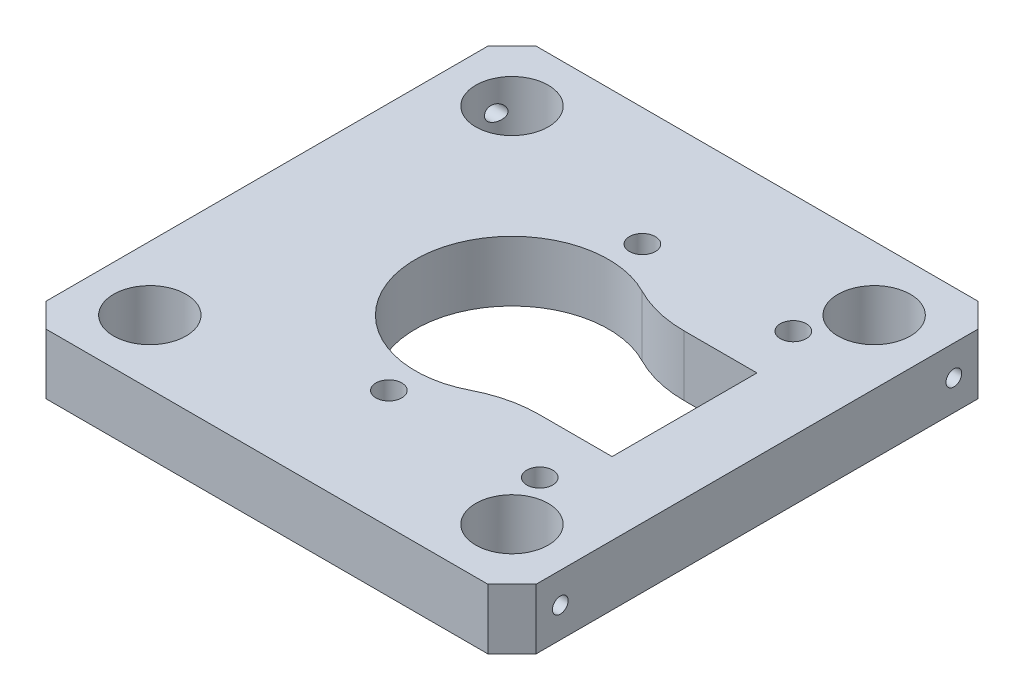
SolidWorks part; units mm, degrees
ref_plane "Front Plane" through (0, 0, 0) normal (0, 0, 1) x (1, 0, 0)
ref_plane "Top Plane" through (0, 0, 0) normal (0, 1, 0) x (1, 0, 0)
ref_plane "Right Plane" through (0, 0, 0) normal (1, 0, 0) x (0, 0, -1)
sketch "Sketch1" plane through (0, 0, 0) normal (0, 1, 0) x (1, 0, 0)
  line L1 (-20.3, -20.3) -> (20.3, -20.3)
  line L2 (-20.3, -20.3) -> (-20.3, 20.3)
  line L3 (-20.3, 20.3) -> (20.3, 20.3)
  line L4 (20.3, -20.3) -> (20.3, 20.3)
  line L5 (-20.3, -20.3) -> (20.3, 20.3) construction
  line L6 (-20.3, 20.3) -> (20.3, -20.3) construction
  point P0 (0, 0)
  dimension "D1" = 40.6
  dimension "D2" = 40.6
extrude "Boss-Extrude1" add sketch "Sketch1" along normal blind 5
sketch "Sketch2" plane through (0, 5, 0) normal (0, 1, 0) x (1, 0, 0)
  line L0 (0, -20.3) -> (0, 20.3) construction
  line L1 (-20.3, -20.3) -> (20.3, -20.3) construction
  line L2 (20.3, 20.3) -> (-20.3, 20.3) construction
  circle A0 centre (0, 0) radius 8
  dimension "D1" = 16
extrude "Cut-Extrude1" cut sketch "Sketch2" against normal blind 5
sketch "Sketch4" plane through (0, 0, 0) normal (0, -1, 0) x (-1, 0, 0)
  line L0 (0, 0) -> (-20.3, 0) construction
  line L1 (-20.3, -20.3) -> (-20.3, 20.3) construction
  line L2 (-5.2915, 6) -> (-14.2915, 6)
  line L3 (-14.2915, 6) -> (-14.2915, 0)
  line L4 (-14.2915, 0) -> (-14.2915, -6)
  line L5 (-14.2915, -6) -> (-5.2915, -6)
  line L6 (-5.2915, -6) -> (-5.2915, 6)
  circle A0 centre (0, 0) radius 8 construction
  dimension "D1" = 6
  dimension "D2" = 6
  dimension "D3" = 9
  dimension "D4" = 9
extrude "Cut-Extrude3" cut sketch "Sketch4" against normal through all
sketch "Sketch5" plane through (0, 5, 0) normal (0, 1, 0) x (1, 0, 0)
  line L0 (-15, 20.3) -> (-15, -20.3) construction
  line L1 (20.3, 20.3) -> (-20.3, 20.3) construction
  line L2 (-20.3, -20.3) -> (20.3, -20.3) construction
  line L3 (15, 20.3) -> (15, -20.3) construction
  line L4 (-20.3, 15) -> (20.3, 15) construction
  line L5 (-20.3, 20.3) -> (-20.3, -20.3) construction
  line L6 (20.3, -20.3) -> (20.3, 20.3) construction
  line L7 (-20.3, -15) -> (20.3, -15) construction
  arc A0 (5.2915, 6) -> (5.2915, -6) centre (0, 0) ccw construction
  circle A1 centre (15, 15) radius 3
  circle A2 centre (15, -15) radius 3
  circle A3 centre (-15, -15) radius 3
  circle A4 centre (-15, 15) radius 3
  dimension "D3" = 15
  dimension "D5" = 6
  dimension "D6" = 6
  dimension "D7" = 6
  dimension "D8" = 6
  dimension "D1" = 30
  dimension "D2" = 30
  dimension "D4" = 15
extrude "Cut-Extrude4" cut sketch "Sketch5" against normal blind 10
chamfer "Chamfer1" distance 2 angle 45 4 edges at (20.3, 2.5, -20.3) (-20.3, 2.5, -20.3) (-20.3, 2.5, 20.3) (20.3, 2.5, 20.3)
sketch "Sketch6" plane through (-20.3, 0, 0) normal (-1, 0, 0) x (0, 0, 1)
  line L0 (-18.3, 5) -> (-18.3, 0) construction
  line L1 (18.3, 0) -> (18.3, 5) construction
  circle A0 centre (-16.3, 2.5) radius 0.65
  circle A1 centre (16.3, 2.5) radius 0.65
  dimension "D1" = 1.3
  dimension "D2" = 2
  dimension "D3" = 1.3
  dimension "D4" = 2
extrude "Cut-Extrude5" cut sketch "Sketch6" against normal blind 5
sketch "Sketch7" plane through (20.3, 0, 0) normal (1, 0, 0) x (0, 0, -1)
  line L0 (-18.3, 5) -> (-18.3, 0) construction
  line L1 (18.3, 0) -> (18.3, 5) construction
  circle A0 centre (16.3, 2.5) radius 0.65
  circle A1 centre (-16.3, 2.5) radius 0.65
  dimension "D1" = 1.3
  dimension "D3" = 1.3
  dimension "D4" = 2
  dimension "D2" = 2
extrude "Cut-Extrude6" cut sketch "Sketch7" against normal blind 5
sketch "Sketch8" plane through (0, 5, 0) normal (0, 1, 0) x (1, 0, 0)
  circle A0 centre (0.3, -10.5) radius 1.075
  circle A1 centre (12.8, -10.5) radius 1.075
  circle A2 centre (0.3, 10.5) radius 1.075
  circle A3 centre (12.8, 10.5) radius 1.075
  dimension "D1" = 2.15
  dimension "D2" = 2.15
  dimension "D3" = 2.15
  dimension "D4" = 2.15
extrude "Cut-Extrude7" cut sketch "Sketch8" against normal blind 10
fillet "Fillet1" radius 10 2 edges at (5.2915, 2.5, 6) (5.2915, 2.5, -6)
